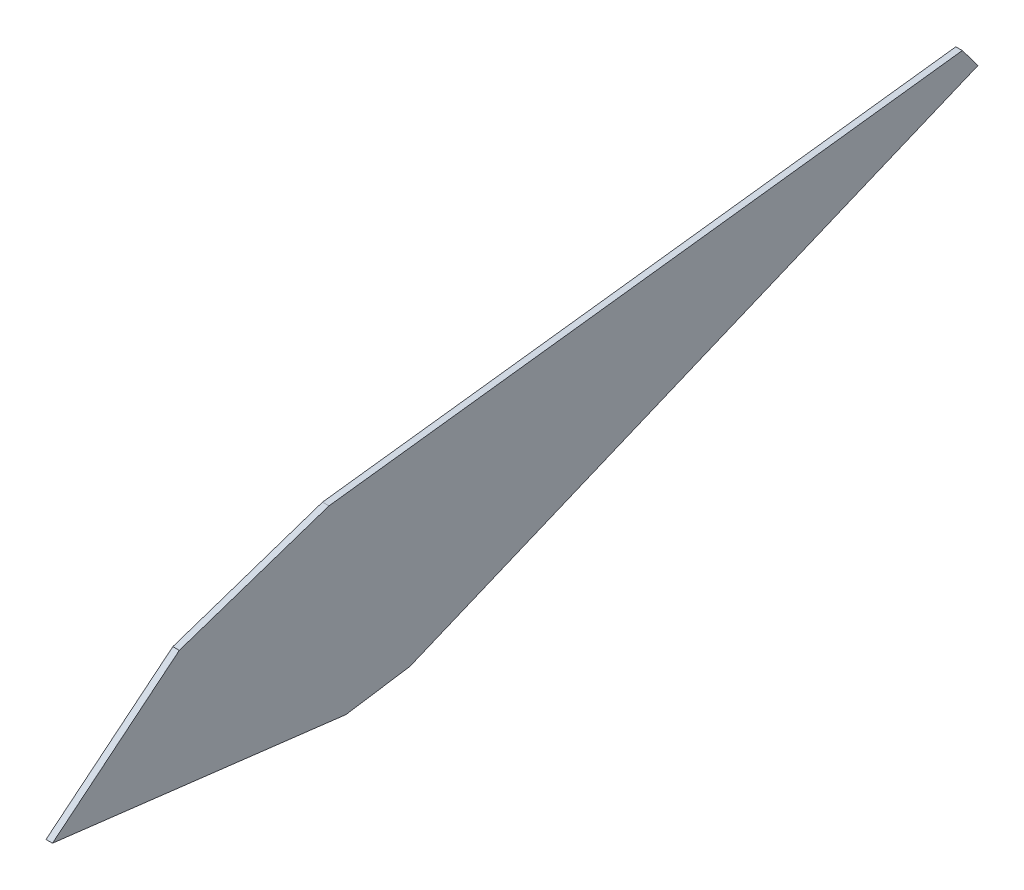
SolidWorks part; units mm, degrees
ref_plane "Front Plane" through (0, 0, 0) normal (0, 0, 1) x (1, 0, 0)
ref_plane "Top Plane" through (0, 0, 0) normal (0, 1, 0) x (1, 0, 0)
ref_plane "Right Plane" through (0, 0, 0) normal (1, 0, 0) x (0, 0, -1)
sketch "Sketch1" plane through (0, 0, 0) normal (1, 0, 0) x (0, 0, -1)
  line L0 (25.4, 5.715) -> (23.8608, 7.7572)
  line L1 (23.8608, 7.7572) -> (-38.2499, 0.1397)
  line L2 (-38.2499, 0.1397) -> (-52.9311, -4.7955)
  line L3 (-52.9311, -4.7955) -> (-65.3694, -14.9555)
  line L4 (-65.3694, -14.9555) -> (-36.5862, -18.4226)
  line L5 (-36.5862, -18.4226) -> (-30.3098, -17.465)
  line L6 (-30.3098, -17.465) -> (25.4, 5.715)
  circle A0 centre (0, 0) radius 0.635 construction
  dimension "D13" = 1.27
  dimension "D1" = 28.7833
  dimension "D2" = 6.2763
  dimension "D3" = 55.7098
  dimension "D4" = 1.5392
  dimension "D5" = 62.1106
  dimension "D6" = 14.6812
  dimension "D7" = 2.0422
  dimension "D8" = 23.18
  dimension "D9" = 0.9576
  dimension "D10" = 3.4671
  dimension "D11" = 10.16
  dimension "D12" = 4.9352
  dimension "D14" = 25.4
  dimension "D15" = 5.715
extrude "Boss-Extrude1" add sketch "Sketch1" along normal blind 0.635
